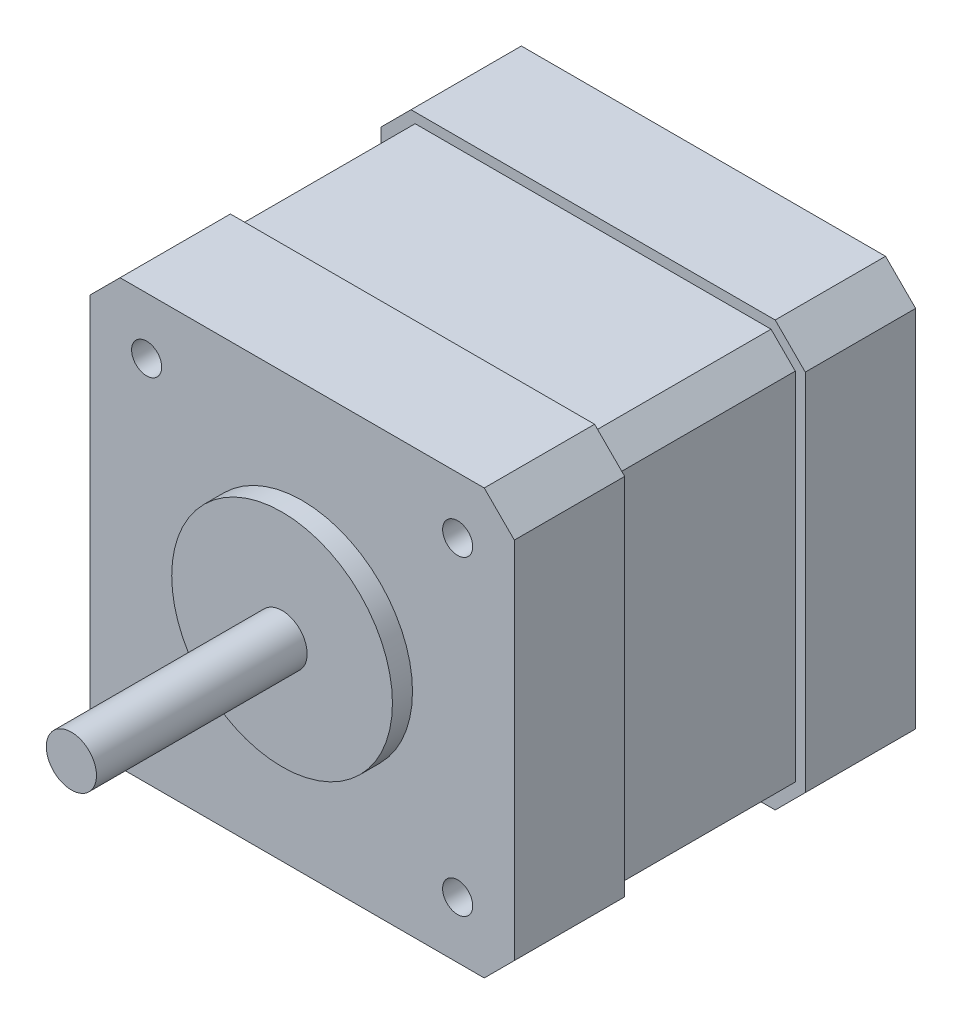
SolidWorks part; units mm, degrees
ref_plane "Спереди" through (0, 0, 0) normal (0, 0, 1) x (1, 0, 0)
ref_plane "Сверху" through (0, 0, 0) normal (0, 1, 0) x (1, 0, 0)
ref_plane "Справа" through (0, 0, 0) normal (1, 0, 0) x (0, 0, -1)
sketch "Эскиз1" plane through (0, 0, 0) normal (0, 0, 1) x (1, 0, 0)
  line L0 (-32.7678, -16.5362) -> (-32.7678, 19.7638)
  line L1 (-29.7678, 22.7638) -> (6.5322, 22.7638)
  line L2 (9.5322, 19.7638) -> (9.5322, -16.5362)
  line L3 (6.5322, -19.5362) -> (-29.7678, -19.5362)
  line L4 (-32.7678, 19.7638) -> (-29.7678, 22.7638)
  line L5 (6.5322, 22.7638) -> (9.5322, 19.7638)
  line L6 (9.5322, -16.5362) -> (6.5322, -19.5362)
  line L7 (-29.7678, -19.5362) -> (-32.7678, -16.5362)
  point P0 (-32.7678, -19.5362)
  point P1 (-32.7678, 22.7638)
  point P2 (9.5322, 22.7638)
  point P3 (9.5322, -19.5362)
extrude "Бобышка-Вытянуть1" add sketch "Эскиз1" along normal blind 10
sketch "Эскиз2" plane through (0, 0, 10) normal (0, 0, 1) x (1, 0, 0)
  circle A0 centre (-11.6178, 1.6138) radius 11
  dimension "D1" = 22
extrude "Бобышка-Вытянуть2" add sketch "Эскиз2" along normal blind 2
sketch "Эскиз3" plane through (0, 0, 12) normal (0, 0, 1) x (1, 0, 0)
  circle A0 centre (-11.6178, 1.6138) radius 2.5
extrude "Бобышка-Вытянуть3" add sketch "Эскиз3" along normal blind 22
sketch "Эскиз6" plane through (0, 0, 0) normal (0, 0, -1) x (-1, 0, 0)
  line L2 (11.6178, 21.7638) -> (-6.118, 21.7638)
  line L4 (-8.5322, 19.3496) -> (-8.5322, -16.122)
  line L5 (-6.5322, -19.5362) -> (-9.5322, -16.5362) construction
  line L6 (-6.118, -18.5362) -> (29.3535, -18.5362)
  line L7 (32.7678, -16.5362) -> (29.7678, -19.5362) construction
  line L9 (31.7678, -16.122) -> (31.7678, 19.3496)
  line L10 (29.7678, 22.7638) -> (32.7678, 19.7638) construction
  line L11 (11.6178, 21.7638) -> (29.3535, 21.7638)
  line L12 (-8.5322, -16.122) -> (-6.118, -18.5362)
  line L13 (-8.5322, 19.3496) -> (-6.118, 21.7638)
  line L14 (-9.5322, 19.7638) -> (-6.5322, 22.7638) construction
  line L15 (29.3535, 21.7638) -> (31.7678, 19.3496)
  line L16 (29.3535, -18.5362) -> (31.7678, -16.122)
  dimension "D1" = 1
  dimension "D2" = 1
  dimension "D3" = 1
  dimension "D4" = 1
extrude "Бобышка-Вытянуть4" add sketch "Эскиз6" along normal blind 18
sketch "Эскиз7" plane through (0, 0, -18) normal (0, 0, 1) x (1, 0, 0)
  line L0 (-32.7678, -16.5362) -> (-32.7678, 19.7638)
  line L1 (-29.7678, 22.7638) -> (6.5322, 22.7638)
  line L2 (9.5322, 19.7638) -> (9.5322, -16.5362)
  line L3 (6.5322, -19.5362) -> (-29.7678, -19.5362)
  line L4 (-32.7678, 19.7638) -> (-29.7678, 22.7638)
  line L5 (6.5322, 22.7638) -> (9.5322, 19.7638)
  line L6 (9.5322, -16.5362) -> (6.5322, -19.5362)
  line L7 (-29.7678, -19.5362) -> (-32.7678, -16.5362)
  point P0 (-32.7678, -19.5362)
  point P1 (-32.7678, 22.7638)
  point P2 (9.5322, 22.7638)
  point P3 (9.5322, -19.5362)
extrude "Бобышка-Вытянуть5" add sketch "Эскиз7" against normal blind 10
sketch "Эскиз4" plane through (0, 0, 10) normal (0, 0, 1) x (1, 0, 0)
  circle A0 centre (-27.1178, 17.1138) radius 1.5
  circle A1 centre (3.8822, 17.1138) radius 1.5
  circle A2 centre (3.8822, -13.8862) radius 1.5
  circle A3 centre (-27.1178, -13.8862) radius 1.5
  point P0 (3.8822, -13.8862)
  point P1 (-27.1178, -13.8862)
  point P14 (-27.1178, 17.1138)
  point P23 (3.8822, 17.1138)
  dimension "D1" = 31
  dimension "D2" = 31
extrude "Вырез-Вытянуть1" cut sketch "Эскиз4" against normal blind 46.5
sketch "Эскиз5" plane through (0, 0, -28) normal (0, 0, -1) x (-1, 0, 0)
  circle A0 centre (11.6178, 1.6138) radius 2.5
extrude "Вырез-Вытянуть2" cut sketch "Эскиз5" against normal blind 1
sketch "Эскиз8" plane through (0, 0, -28) normal (0, 0, -1) x (-1, 0, 0)
  line L0 (11.6178, 1.6138) -> (32.7678, 1.6138) construction
  line L1 (32.7678, 19.7638) -> (32.7678, -16.5362) construction
  line L2 (11.6178, 1.6138) -> (11.6178, 22.7638) construction
  line L3 (-6.5322, 22.7638) -> (29.7678, 22.7638) construction
  circle A0 centre (11.6178, 1.6138) radius 2.5 construction
  circle A1 centre (11.6178, 1.6138) radius 2.5 construction
  point P4 (11.6178, 1.6138)
ref_plane "А" through (0, 1.6138, 0) normal (0, -1, 0) x (-1, 0, 0)
ref_plane "Б" through (-11.6178, 0, 0) normal (-1, 0, 0) x (0, 1, 0)
sketch "Эскиз9" plane through (0, 0, 10) normal (0, 0, 1) x (1, 0, 0)
  line L8 (-29.7678, 22.7638) -> (-32.7678, 19.7638)
  line L9 (-32.7678, 19.7638) -> (-32.7678, -16.5362)
  line L10 (-32.7678, -16.5362) -> (-29.7678, -19.5362)
  line L11 (-29.7678, -19.5362) -> (6.5322, -19.5362)
  line L12 (6.5322, -19.5362) -> (9.5322, -16.5362)
  line L13 (9.5322, -16.5362) -> (9.5322, 19.7638)
  line L14 (9.5322, 19.7638) -> (6.5322, 22.7638)
  line L15 (6.5322, 22.7638) -> (-29.7678, 22.7638)
  line L16 (-29.7678, 22.7638) -> (-32.7678, 19.7638)
  line L17 (-32.7678, 19.7638) -> (-32.7678, -16.5362)
  line L18 (-32.7678, -16.5362) -> (-29.7678, -19.5362)
  line L19 (-29.7678, -19.5362) -> (6.5322, -19.5362)
  line L20 (6.5322, -19.5362) -> (9.5322, -16.5362)
  line L21 (9.5322, -16.5362) -> (9.5322, 19.7638)
  line L22 (9.5322, 19.7638) -> (6.5322, 22.7638)
  line L23 (6.5322, 22.7638) -> (-29.7678, 22.7638)
  circle A0 centre (3.8822, 17.1138) radius 1.5 construction
  circle A1 centre (3.8822, -13.8862) radius 1.5 construction
  circle A2 centre (-27.1178, -13.8862) radius 1.5 construction
  circle A3 centre (-27.1178, 17.1138) radius 1.5 construction
  circle A4 centre (3.8822, 17.1138) radius 1.5
  circle A5 centre (3.8822, -13.8862) radius 1.5
  circle A6 centre (-27.1178, -13.8862) radius 1.5
  circle A7 centre (-27.1178, 17.1138) radius 1.5
  dimension "D1" = 0
extrude "Бобышка-Вытянуть6" add sketch "Эскиз9" along normal blind 1
sketch "Эскиз10" plane through (0, 0, -28) normal (0, 0, -1) x (-1, 0, 0)
  line L8 (32.7678, 19.7638) -> (29.7678, 22.7638)
  line L9 (29.7678, 22.7638) -> (-6.5322, 22.7638)
  line L10 (-6.5322, 22.7638) -> (-9.5322, 19.7638)
  line L11 (-9.5322, 19.7638) -> (-9.5322, -16.5362)
  line L12 (-9.5322, -16.5362) -> (-6.5322, -19.5362)
  line L13 (-6.5322, -19.5362) -> (29.7678, -19.5362)
  line L14 (29.7678, -19.5362) -> (32.7678, -16.5362)
  line L15 (32.7678, -16.5362) -> (32.7678, 19.7638)
  line L16 (32.7678, 19.7638) -> (29.7678, 22.7638)
  line L17 (29.7678, 22.7638) -> (-6.5322, 22.7638)
  line L18 (-6.5322, 22.7638) -> (-9.5322, 19.7638)
  line L19 (-9.5322, 19.7638) -> (-9.5322, -16.5362)
  line L20 (-9.5322, -16.5362) -> (-6.5322, -19.5362)
  line L21 (-6.5322, -19.5362) -> (29.7678, -19.5362)
  line L22 (29.7678, -19.5362) -> (32.7678, -16.5362)
  line L23 (32.7678, -16.5362) -> (32.7678, 19.7638)
  circle A0 centre (-3.8822, -13.8862) radius 1.5 construction
  circle A1 centre (27.1178, -13.8862) radius 1.5 construction
  circle A2 centre (11.6178, 1.6138) radius 2.5 construction
  circle A3 centre (-3.8822, 17.1138) radius 1.5 construction
  circle A4 centre (27.1178, 17.1138) radius 1.5 construction
  circle A5 centre (-3.8822, -13.8862) radius 1.5
  circle A6 centre (27.1178, -13.8862) radius 1.5
  circle A7 centre (11.6178, 1.6138) radius 2.5
  circle A8 centre (-3.8822, 17.1138) radius 1.5
  circle A9 centre (27.1178, 17.1138) radius 1.5
  dimension "D1" = 0
extrude "Бобышка-Вытянуть7" add sketch "Эскиз10" along normal blind 1
sketch "Эскиз11" plane through (0, 0, 12) normal (0, 0, 1) x (1, 0, 0)
  circle A0 centre (-11.6178, 1.6138) radius 2.5 construction
  circle A1 centre (-11.6178, 1.6138) radius 11
  circle A2 centre (-11.6178, 1.6138) radius 11
  circle A3 centre (-11.6178, 1.6138) radius 2.5
  dimension "D1" = 0
extrude "Бобышка-Вытянуть8" add sketch "Эскиз11" along normal blind 1
